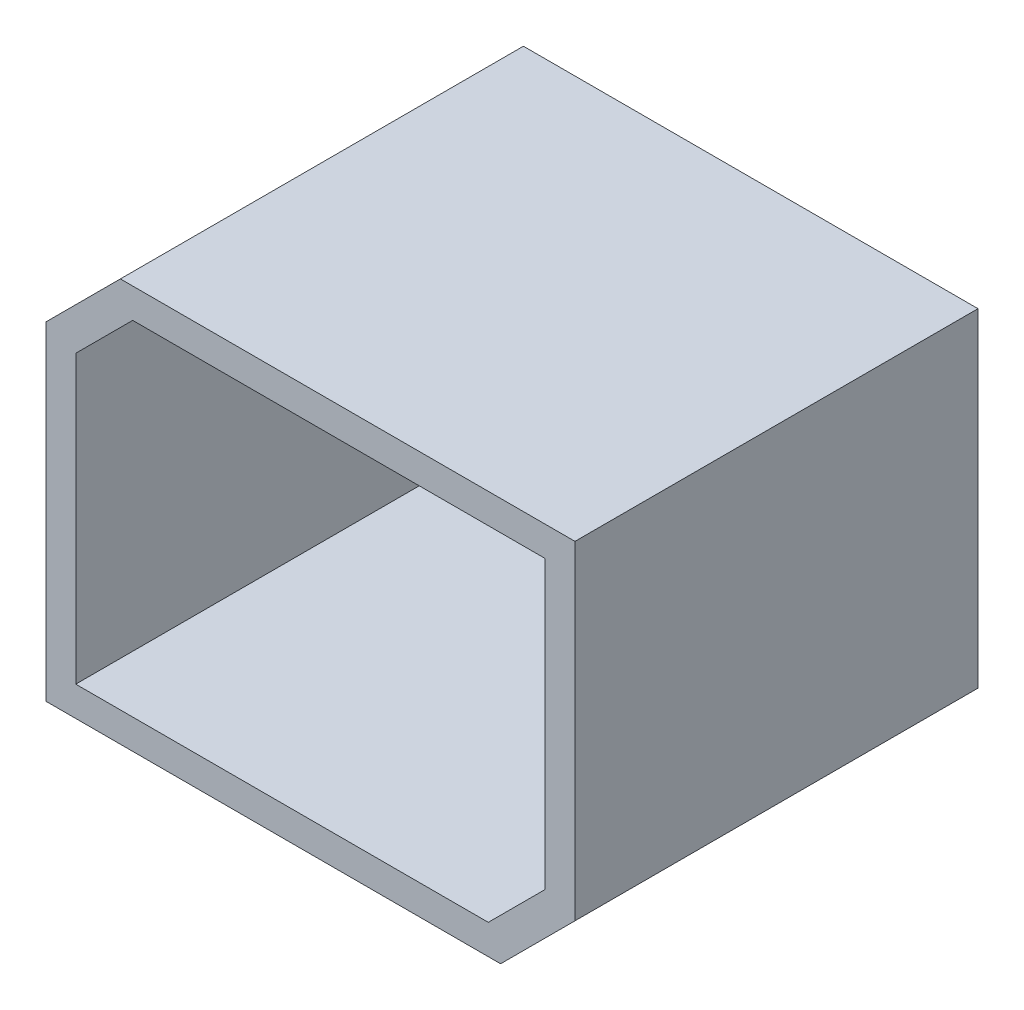
SolidWorks part; units mm, degrees
ref_plane "Front Plane" through (0, 0, 0) normal (0, 0, 1) x (1, 0, 0)
ref_plane "Top Plane" through (0, 0, 0) normal (0, 1, 0) x (1, 0, 0)
ref_plane "Right Plane" through (0, 0, 0) normal (1, 0, 0) x (0, 0, -1)
sketch "Sketch1" plane through (0, 0, 0) normal (0, 0, 1) x (1, 0, 0)
  line L1 (0, 0) -> (106.68, 0)
  line L2 (0, 0) -> (0, 81.28)
  line L3 (0, 81.28) -> (106.68, 81.28)
  line L4 (106.68, 0) -> (106.68, 81.28)
  dimension "D1" = 81.28
  dimension "D2" = 106.68
extrude "Boss-Extrude1" add sketch "Sketch1" along normal blind 81.28
chamfer "Chamfer1" distance 15 angle 45 2 edges at (106.68, 0, 40.64) (0, 81.28, 40.64)
shell "Shell2" thickness 6
